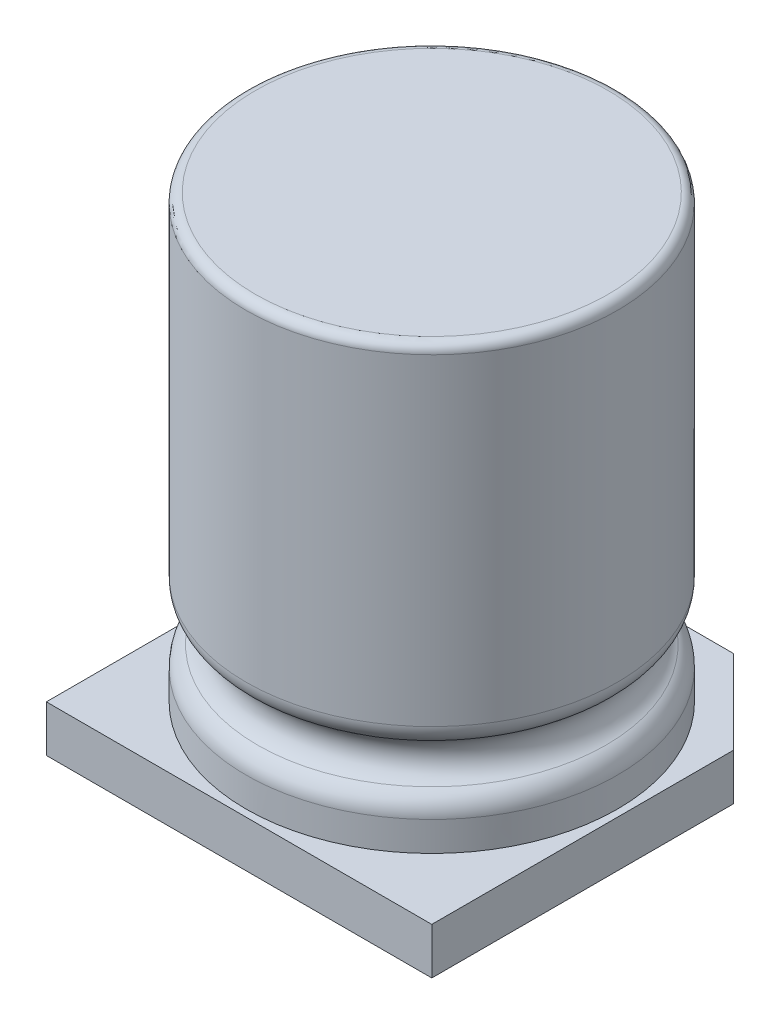
SolidWorks part; units mm, degrees
ref_plane "Front Plane" through (0, 0, 0) normal (0, 0, 1) x (1, 0, 0)
ref_plane "Top Plane" through (0, 0, 0) normal (0, 1, 0) x (1, 0, 0)
ref_plane "Right Plane" through (0, 0, 0) normal (1, 0, 0) x (0, 0, -1)
sketch "Sketch1" plane through (0, 0, 0) normal (0, 1, 0) x (1, 0, 0)
  line L1 (-4.15, 4.15) -> (4.15, 4.15)
  line L2 (-4.15, 4.15) -> (-4.15, -4.15)
  line L3 (-4.15, -4.15) -> (4.15, -4.15)
  line L4 (4.15, 4.15) -> (4.15, -4.15)
  line L5 (-4.15, 4.15) -> (4.15, -4.15) construction
  line L6 (-4.15, -4.15) -> (4.15, 4.15) construction
  point P0 (0, 0)
  dimension "D1" = 8.3
extrude "Boss-Extrude1" add sketch "Sketch1" along normal blind 1
sketch "Sketch2" plane through (0, 1, 0) normal (0, 1, 0) x (1, 0, 0)
  circle A0 centre (0, 0) radius 4
  dimension "D1" = 8
extrude "Boss-Extrude2" add sketch "Sketch2" along normal blind 9.5 separate body
sketch "Sketch3" plane through (0, 0, 0) normal (0, 0, 1) x (1, 0, 0)
  line L0 (4, 1) -> (4, 2.5) construction
  circle A0 centre (4, 2.5) radius 0.5
  point P2 (4, 2)
  dimension "D1" = 1
  dimension "D2" = 1
revolve "Cut-Revolve1" cut sketch "Sketch3" angle 360 about axis through (0, 10.5, 0) along (0, -1, 0)
fillet "Fillet1" radius 0.5 2 edges at (0, 2, 4) (0, 3, -4)
fillet "Fillet2" radius 0.2 1 edges at (0, 10.5, 4)
chamfer "Chamfer1" distance 1.8 angle 45 2 edges at (4.15, 0.5, -4.15) (-4.15, 0.5, -4.15)
